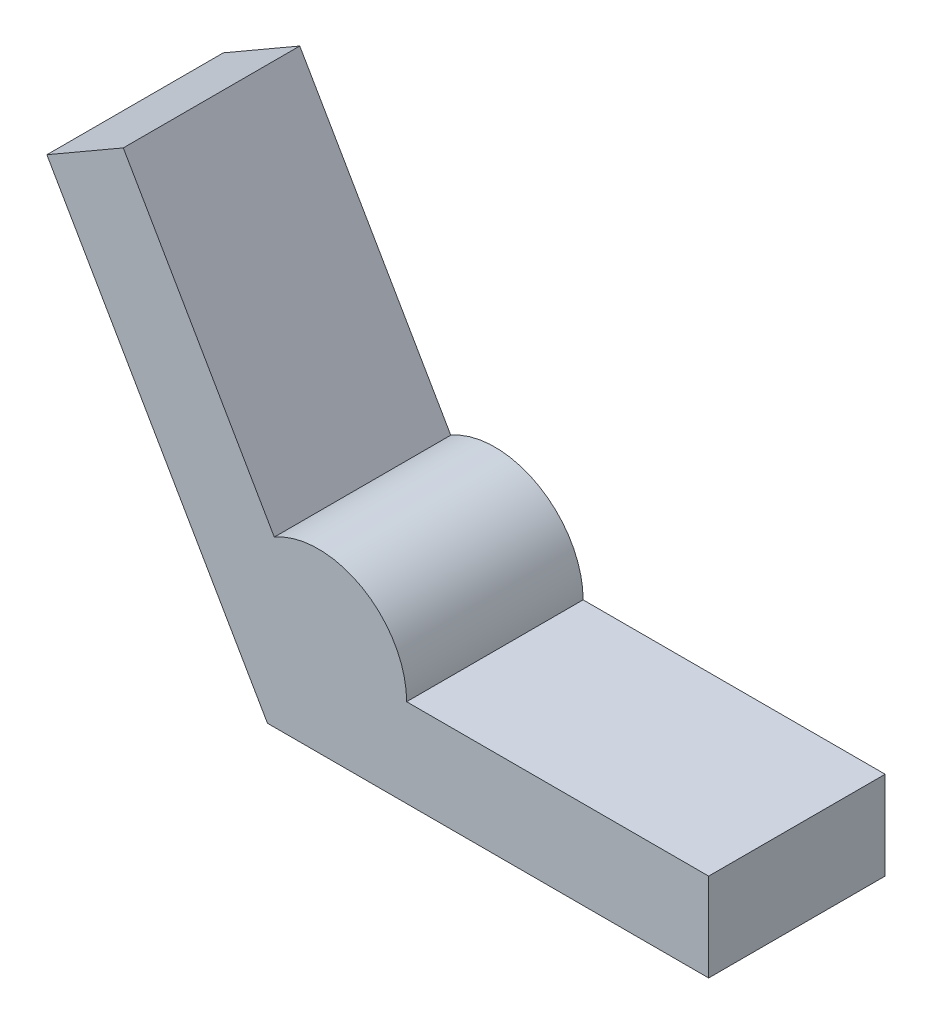
SolidWorks part; units mm, degrees
ref_plane "정면" through (0, 0, 0) normal (0, 0, 1) x (1, 0, 0)
ref_plane "윗면" through (0, 0, 0) normal (0, 1, 0) x (1, 0, 0)
ref_plane "우측면" through (0, 0, 0) normal (1, 0, 0) x (0, 0, -1)
sketch "Sketch1" plane through (0, 0, 0) normal (0, 0, 1) x (1, 0, 0)
  line L0 (0, 19.844) -> (0, -19.789) construction
  line L1 (0, 0) -> (15, 0)
  line L2 (15, 0) -> (15, 3)
  line L3 (15, 3) -> (4.7321, 3)
  line L4 (0.2321, 5.5981) -> (-4.9019, 14.4904)
  line L5 (-4.9019, 14.4904) -> (-7.5, 12.9904)
  line L6 (-7.5, 12.9904) -> (0, 0)
  arc A0 (4.7321, 3) -> (0.2321, 5.5981) centre (1.7321, 3) ccw
  point P11 (0, 0)
  point P12 (0, 0)
  point P13 (0, 0)
  point P14 (-1.6195, 0)
  point P15 (0, 0)
  point P16 (0, 0)
  dimension "D1" = 3
  dimension "D7" = 3
  dimension "D2" = 3
  dimension "D3" = 120
  dimension "D4" = 120
  dimension "D5" = 15
  dimension "D6" = 15
extrude "Boss-Extrude1" add sketch "Sketch1" along normal blind 6
